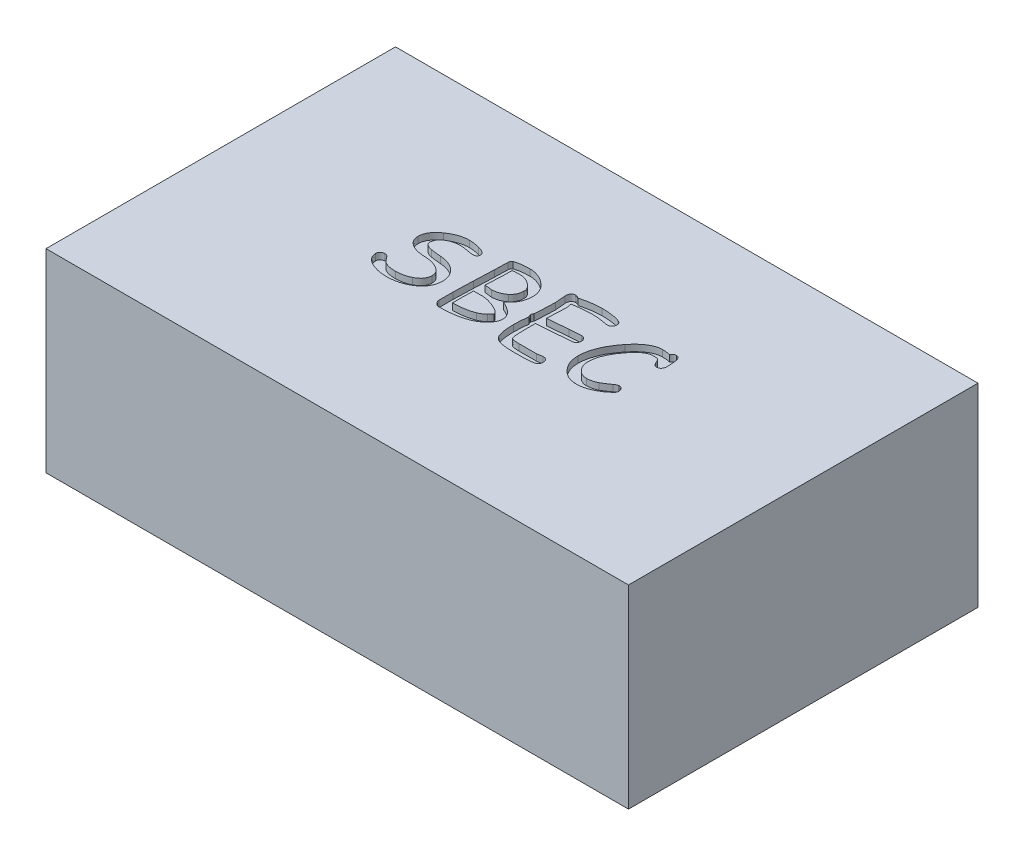
SolidWorks part; units mm, degrees
material "uhlíková ocel 7850"
ref_plane "Přední rovina" through (0, 0, 0) normal (0, 0, 1) x (1, 0, 0)
ref_plane "Horní rovina" through (0, 0, 0) normal (0, 1, 0) x (1, 0, 0)
ref_plane "Pravá rovina" through (0, 0, 0) normal (1, 0, 0) x (0, 0, -1)
sketch "Skica1" plane through (0, 0, 0) normal (0, 1, 0) x (1, 0, 0)
  line L1 (22.5, -13.5) -> (-22.5, -13.5)
  line L2 (22.5, -13.5) -> (22.5, 13.5)
  line L3 (22.5, 13.5) -> (-22.5, 13.5)
  line L4 (-22.5, -13.5) -> (-22.5, 13.5)
  line L5 (22.5, -13.5) -> (-22.5, 13.5) construction
  line L6 (22.5, 13.5) -> (-22.5, -13.5) construction
  point P0 (0, 0)
  dimension "D1" = 27
  dimension "D2" = 45
extrude "Přidat vysunutím1" add sketch "Skica1" along normal blind 15
sketch "Skica2" plane through (0, 15, 0) normal (0, 1, 0) x (1, 0, 0)
  text T0 "SBEC" font "Comic Sans MS" height in points 20
extrude "Odebrat vysunutím1" cut sketch "Skica2" against normal blind 0.5
